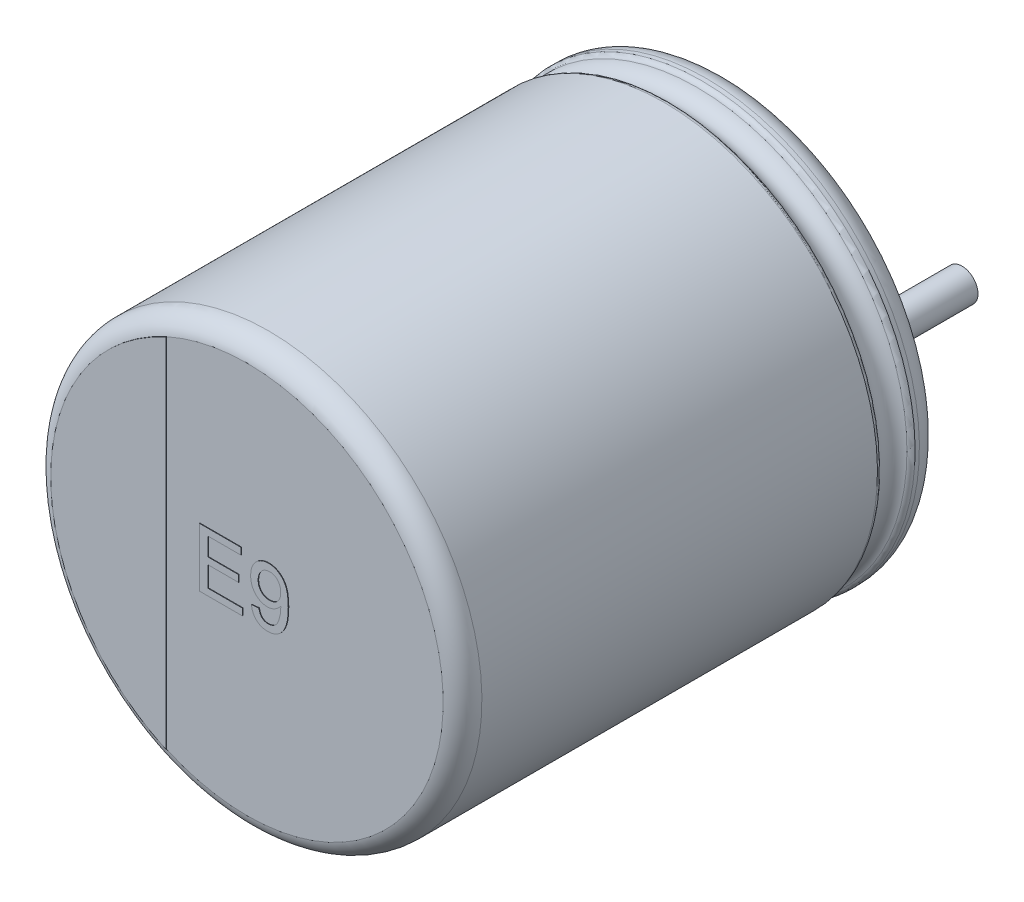
SolidWorks part; units mm, degrees
ref_plane "Plan de face" through (0, 0, 0) normal (0, 0, 1) x (1, 0, 0)
ref_plane "Plan de dessus" through (0, 0, 0) normal (0, 1, 0) x (1, 0, 0)
ref_plane "Plan de droite" through (0, 0, 0) normal (1, 0, 0) x (0, 0, -1)
sketch "Sketch10" plane through (0, 0, 0) normal (1, 0, 0) x (0, 0, -1)
  line L0 (18.1631, 0) -> (-18.9631, 0) construction
  line L1 (-9, 0) -> (-0.05, 0)
  line L2 (-9, 0) -> (-9, 3.6736)
  line L3 (-8.6, 4) -> (-1.1846, 4)
  line L4 (-0.05, 3.4031) -> (-0.05, 0)
  line L7 (-0.4794, 4) -> (-0.3982, 4)
  arc A0 (-9, 3.6736) -> (-8.6, 4) centre (-8.6068, 3.6001) cw
  arc A1 (-0.3982, 4) -> (-0.05, 3.4031) centre (-0.3982, 3.6) cw
  arc A2 (-0.5713, 3.9394) -> (-1.0926, 3.9394) centre (-0.832, 4.051) cw
  arc A3 (-1.0926, 3.9394) -> (-1.1846, 4) centre (-1.1846, 3.9) ccw
  arc A4 (-0.5713, 3.9394) -> (-0.4794, 4) centre (-0.4794, 3.9) cw
  point P4 (0.57, 0)
  point P13 (-9, 4)
  dimension "D2" = 0.4
  dimension "D3" = 0.4
  dimension "D4" = 0.1
  dimension "D5" = 0.1
  dimension "D1" = 4
revolve "Повернуть1" add sketch "Sketch10" angle 360 about L0
sketch "Эскиз2" plane through (0, 0, 0.05) normal (0, 0, -1) x (-1, 0, 0)
  line L1 (0, 0.7993) -> (0, -1.0496) construction
  line L2 (-1.75, 0) -> (3.1313, 0) construction
  circle A3 centre (-1.75, 0) radius 0.3
  circle A7 centre (1.75, 0) radius 0.3
  dimension "D1" = 3.5
extrude "Бобышка-Вытянуть1" add sketch "Эскиз2" along normal blind 2.7
sketch "Эскиз4" plane through (0, 0, 9) normal (0, 0, 1) x (1, 0, 0)
  line L0 (-1.5096, -3.3491) -> (-1.5096, 3.3491)
  circle A1 centre (0, 0) radius 3.6736 construction
  arc A2 (-1.5096, 3.3491) -> (-1.5096, -3.3491) centre (0, 0) ccw
extrude "Бобышка-Вытянуть2" add sketch "Эскиз4" along normal blind 0.01
sketch "Эскиз5" plane through (0, 0, 9) normal (0, 0, 1) x (1, 0, 0)
  text T0 "E9" font "Arial" height 1.1
extrude "Текст" add sketch "Эскиз5" along normal blind 0.01
sketch "Эскиз6" plane through (0, 0, 0.05) normal (0, 0, -1) x (-1, 0, 0)
  line L0 (-1.75, 0.4656) -> (-2.1332, 0.4656)
  line L1 (-1.75, -0.4656) -> (-2.1332, -0.4656)
  line L2 (1.75, -0.4656) -> (2.1332, -0.4656)
  line L3 (1.75, 0.4656) -> (2.1332, 0.4656)
  arc A0 (-2.3702, -0.7952) -> (2.3702, -0.7952) centre (0, 0) ccw
  arc A1 (-1.75, -0.4656) -> (-1.75, 0.4656) centre (-1.75, 0) ccw
  arc A2 (1.75, 0.4656) -> (1.75, -0.4656) centre (1.75, 0) ccw
  arc A3 (2.3702, 0.7952) -> (-2.3702, 0.7952) centre (0, 0) ccw
  arc A4 (2.1332, 0.4656) -> (2.3702, 0.7952) centre (2.1332, 0.7156) ccw
  arc A5 (2.1332, -0.4656) -> (2.3702, -0.7952) centre (2.1332, -0.7156) cw
  arc A6 (-2.3702, -0.7952) -> (-2.1332, -0.4656) centre (-2.1332, -0.7156) cw
  arc A7 (-2.1332, 0.4656) -> (-2.3702, 0.7952) centre (-2.1332, 0.7156) cw
  point P7 (2.4563, 0.4656)
  point P23 (0, -2.5)
  point P24 (0, 2.5)
  dimension "D1" = 0.25
  dimension "D2" = 5
extrude "Бобышка-Вытянуть5" add sketch "Эскиз6" along normal blind 0.05 contours A3 A7 L0 A1 L1 A6 A0 A5 L2 A2 L3 A4
